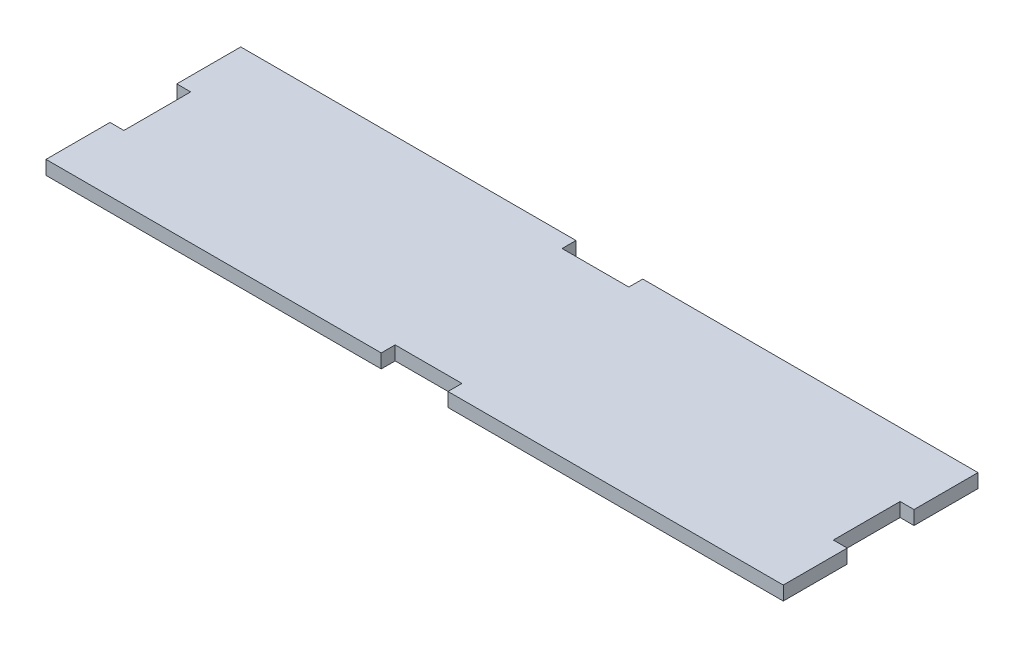
SolidWorks part; units mm, degrees
ref_plane "Front Plane" through (0, 0, 0) normal (0, 0, 1) x (1, 0, 0)
ref_plane "Top Plane" through (0, 0, 0) normal (0, 1, 0) x (1, 0, 0)
ref_plane "Right Plane" through (0, 0, 0) normal (1, 0, 0) x (0, 0, -1)
sketch "Sketch1" plane through (0, 0, 0) normal (0, 1, 0) x (1, 0, 0)
  line L1 (0, 0) -> (-336.55, 0)
  line L2 (0, 0) -> (0, -88.9)
  line L3 (0, -88.9) -> (-336.55, -88.9)
  line L4 (-336.55, 0) -> (-336.55, -88.9)
  dimension "D1" = 336.55
  dimension "D2" = 88.9
extrude "Boss-Extrude1" add sketch "Sketch1" along normal blind 6.35
sketch "Sketch2" plane through (0, 6.35, 0) normal (0, 1, 0) x (1, 0, 0)
  line L0 (0, 0) -> (-336.55, 0) construction
  line L1 (-183.515, 0) -> (-153.035, 0)
  line L2 (-183.515, 0) -> (-183.515, -6.35)
  line L3 (-183.515, -6.35) -> (-153.035, -6.35)
  line L4 (-153.035, 0) -> (-153.035, -6.35)
  line L5 (-336.55, -88.9) -> (0, -88.9) construction
  line L6 (-183.515, -88.9) -> (-153.035, -88.9)
  line L7 (-183.515, -88.9) -> (-183.515, -82.55)
  line L8 (-183.515, -82.55) -> (-153.035, -82.55)
  line L9 (-153.035, -88.9) -> (-153.035, -82.55)
  line L10 (0, -88.9) -> (0, 0) construction
  line L11 (0, -59.69) -> (-6.35, -59.69)
  line L12 (0, -59.69) -> (0, -29.21)
  line L13 (0, -29.21) -> (-6.35, -29.21)
  line L14 (-6.35, -59.69) -> (-6.35, -29.21)
  line L15 (-336.55, 0) -> (-336.55, -88.9) construction
  line L16 (-336.55, -29.21) -> (-330.2, -29.21)
  line L17 (-336.55, -29.21) -> (-336.55, -59.69)
  line L18 (-336.55, -59.69) -> (-330.2, -59.69)
  line L19 (-330.2, -29.21) -> (-330.2, -59.69)
  point P24 (-330.2, -44.45)
  point P25 (-336.55, -44.45)
  point P26 (0, -44.45)
  point P27 (0, -44.45)
  point P28 (-168.275, 0)
  point P29 (-168.275, 0)
  point P30 (-168.275, -88.9)
  point P31 (-168.275, -88.9)
  dimension "D1" = 15.24
  dimension "D2" = 6.35
  dimension "D3" = 0
  dimension "D4" = 6.35
  dimension "D5" = 0
  dimension "D6" = 30.48
  dimension "D7" = 6.35
  dimension "D8" = 30.48
  dimension "D9" = 0
  dimension "D10" = 30.48
  dimension "D11" = 6.35
  dimension "D12" = 0
extrude "Cut-Extrude1" cut sketch "Sketch2" against normal through all
